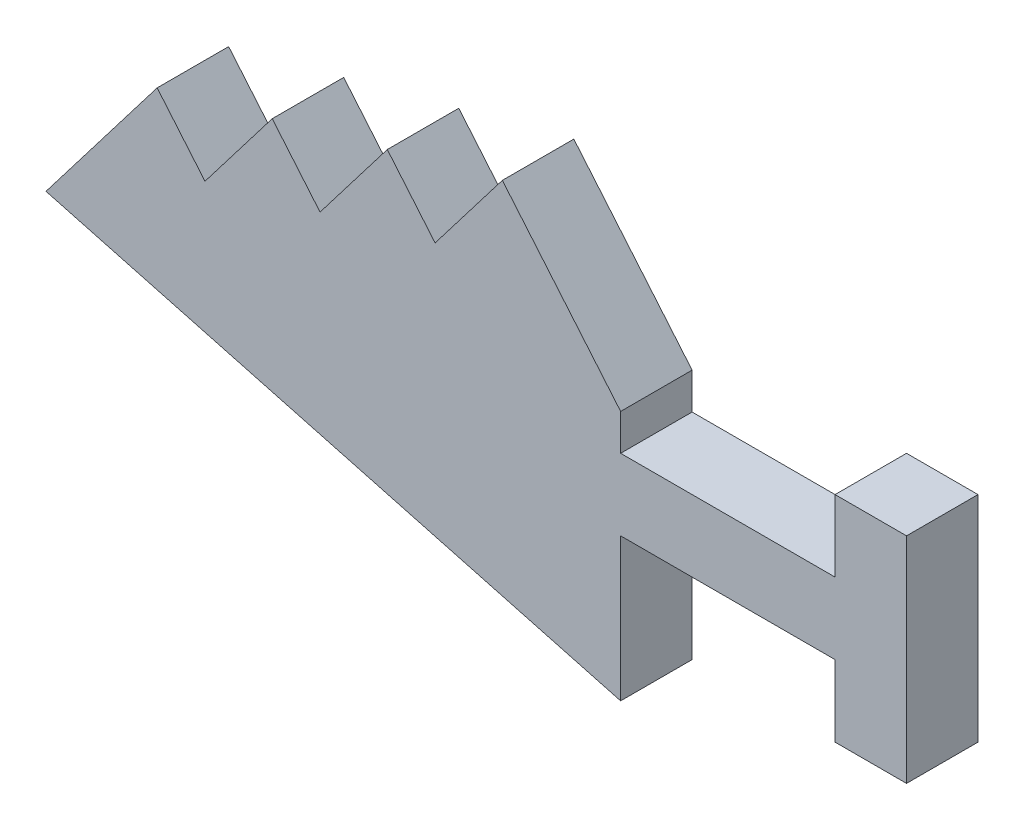
SolidWorks part; units mm, degrees
ref_plane "Front Plane" through (0, 0, 0) normal (0, 0, 1) x (1, 0, 0)
ref_plane "Top Plane" through (0, 0, 0) normal (0, 1, 0) x (1, 0, 0)
ref_plane "Right Plane" through (0, 0, 0) normal (1, 0, 0) x (0, 0, -1)
sketch "Model" plane through (0, 0, 0) normal (0, 0, 1) x (1, 0, 0)
  line L0 (50.4572, 33.0986) -> (56.1018, 40.4712)
  line L1 (50.4572, 33.0986) -> (46.4426, 37.883)
  line L2 (40.7979, 30.5104) -> (46.4426, 37.883)
  line L3 (40.7979, 30.5104) -> (36.7833, 35.2948)
  line L4 (31.1387, 27.9222) -> (36.7833, 35.2948)
  line L5 (31.1387, 27.9222) -> (27.124, 32.7066)
  line L6 (19.1979, 22.354) -> (27.124, 32.7066)
  line L7 (66.0319, 28.6369) -> (66.0319, 25.5917)
  line L8 (66.0319, 19.5917) -> (84.0319, 19.5917)
  line L9 (90.0319, 13.5917) -> (84.0319, 13.5917)
  line L10 (84.0319, 13.5917) -> (84.0319, 19.5917)
  line L11 (90.0319, 31.5917) -> (84.0319, 31.5917)
  line L12 (84.0319, 31.5917) -> (84.0319, 25.5917)
  line L13 (84.0319, 25.5917) -> (66.0319, 25.5917)
  line L14 (56.1018, 40.4712) -> (66.0319, 28.6369)
  line L15 (66.0319, 7.5917) -> (17.7919, 20.5176)
  line L16 (19.1979, 22.354) -> (17.7919, 20.5176)
  line L17 (66.0319, 7.5917) -> (66.0319, 19.5917)
  line L18 (90.0319, 31.5917) -> (90.0319, 13.5917)
extrude "Boss-Extrude1" add sketch "Model" along normal blind 6 contours L6 L5 L4 L3 L2 L1 L0 L14 L7 L13 L12 L11 L18 L9 L10 L8 L17 L15 L16
